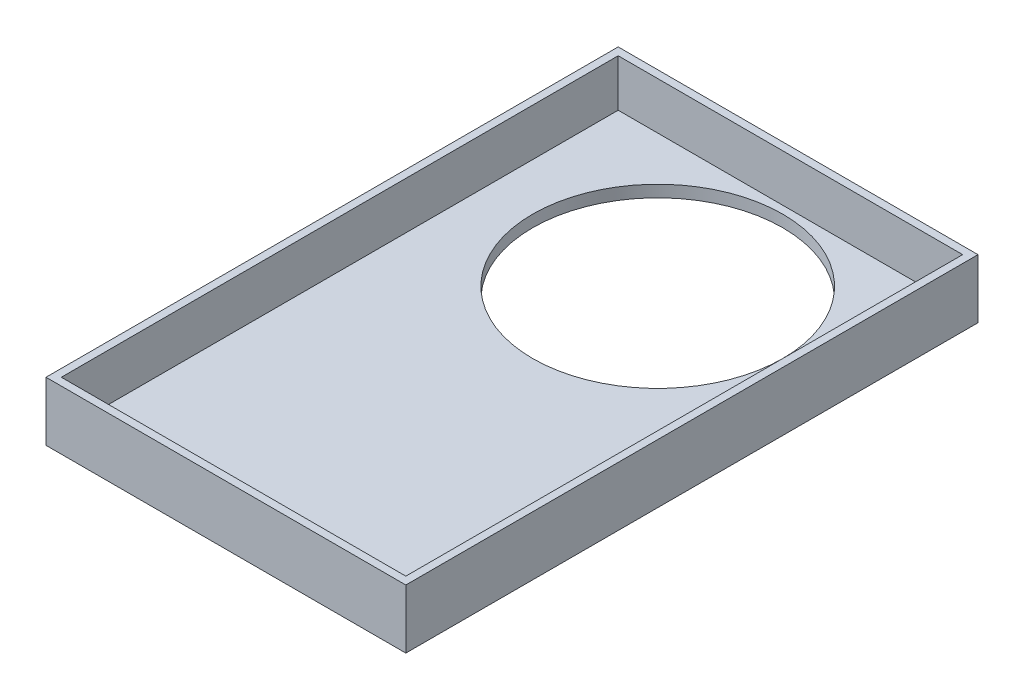
SolidWorks part; units mm, degrees
ref_plane "Front Plane" through (0, 0, 0) normal (0, 0, 1) x (1, 0, 0)
ref_plane "Top Plane" through (0, 0, 0) normal (0, 1, 0) x (1, 0, 0)
ref_plane "Right Plane" through (0, 0, 0) normal (1, 0, 0) x (0, 0, -1)
sketch "Sketch1" plane through (0, 0, 0) normal (0, 1, 0) x (1, 0, 0)
  line L0 (14.25, -10.5939) -> (15.25, -10.5939) construction
  line L5 (-14.25, 12.6561) -> (14.25, 12.6561)
  line L6 (-14.25, 12.6561) -> (-14.25, -33.8439)
  line L11 (-14.25, -33.8439) -> (14.25, -33.8439)
  line L12 (14.25, 12.6561) -> (14.25, -33.8439)
  line L13 (14.75, -10.5939) -> (14.75, 7.2968) construction
  line L15 (15.25, 12.8561) -> (44.15, 12.8561)
  line L16 (15.25, 12.8561) -> (15.25, -34.0439)
  line L17 (15.25, -34.0439) -> (44.15, -34.0439)
  line L18 (44.15, 12.8561) -> (44.15, -34.0439)
  line L19 (-15.25, 13.6561) -> (46.15, 13.6561)
  line L20 (-15.25, 13.6561) -> (-15.25, -34.8439)
  line L21 (-15.25, -34.8439) -> (46.15, -34.8439)
  line L22 (46.15, 13.6561) -> (46.15, -34.8439)
  circle A0 centre (0, 0) radius 10.25
  dimension "D1" = 28.5
  dimension "D2" = 14.25
  dimension "D3" = 46.5
  dimension "D4" = 1
  dimension "D5" = 28.9
  dimension "D6" = 46.9
  dimension "D7" = 1
  dimension "D8" = 1
  dimension "D9" = 1
  dimension "D10" = 2
extrude "Boss-Extrude1" add sketch "Sketch1" along normal blind 35.7 contours L22 L19 L20 L21 L5 L12 L11 L6 L15 L18 L17 L16
sketch "Sketch2" plane through (0, 35.7, 0) normal (0, 1, 0) x (1, 0, 0)
  line L0 (-15.25, -34.8439) -> (46.15, -34.8439) construction
  line L1 (46.15, 13.6561) -> (16.25, 13.6561)
  line L2 (46.15, 13.6561) -> (46.15, -34.8439)
  line L3 (46.15, -34.8439) -> (16.25, -34.8439)
  line L4 (16.25, 13.6561) -> (16.25, -34.8439)
extrude "Cut-Extrude1" cut sketch "Sketch2" against normal through all
sketch "Sketch3" plane through (0, 35.7, 0) normal (0, 1, 0) x (1, 0, 0)
  line L0 (-14.25, 12.6561) -> (14.25, 12.6561) construction
  line L1 (-14.6, 13.0061) -> (14.6, 13.0061)
  line L2 (-14.6, 13.0061) -> (-14.6, -34.1939)
  line L3 (-14.6, -34.1939) -> (14.6, -34.1939)
  line L4 (14.6, 13.0061) -> (14.6, -34.1939)
  line L5 (-14.25, 12.6561) -> (-14.25, -33.8439) construction
  line L6 (14.25, 12.6561) -> (14.25, -33.8439) construction
  line L7 (-14.25, -33.8439) -> (14.25, -33.8439) construction
  dimension "D1" = 0.35
  dimension "D2" = 0.35
  dimension "D3" = 0.35
  dimension "D4" = 0.35
extrude "Cut-Extrude2" cut sketch "Sketch3" against normal through all
sketch "Sketch4" plane through (0, 0, 0) normal (0, 1, 0) x (1, 0, 0)
  line L1 (-14.6, 13.0061) -> (14.6, 13.0061)
  line L2 (-14.6, 13.0061) -> (-14.6, -34.1939)
  line L3 (-14.6, -34.1939) -> (14.6, -34.1939)
  line L4 (14.6, 13.0061) -> (14.6, -34.1939)
  circle A1 centre (0, 1.7561) radius 10.6
  dimension "D1" = 21.2
  dimension "D2" = 11.25
  dimension "D3" = 14.6
extrude "Boss-Extrude2" add sketch "Sketch4" along normal blind 1
sketch "Sketch6" plane through (0, 35.7, 0) normal (0, 1, 0) x (1, 0, 0)
  line L0 (-15.25, -34.8439) -> (16.25, -34.8439) construction
  line L1 (16.25, 13.6561) -> (15.25, 13.6561)
  line L2 (16.25, 13.6561) -> (16.25, -34.8439)
  line L3 (16.25, -34.8439) -> (15.25, -34.8439)
  line L4 (15.25, 13.6561) -> (15.25, -34.8439)
extrude "Cut-Extrude3" cut sketch "Sketch6" against normal through all
sketch "Sketch7" plane through (0, 0, 34.8439) normal (0, 0, 1) x (1, 0, 0)
  line L0 (15.25, 0) -> (15.25, 35.7) construction
  line L1 (-15.25, 35.7) -> (15.25, 35.7)
  line L2 (-15.25, 35.7) -> (-15.25, 5)
  line L3 (-15.25, 5) -> (15.25, 5)
  line L4 (15.25, 35.7) -> (15.25, 5)
  line L5 (-15.25, 0) -> (15.25, 0) construction
  dimension "D1" = 5
extrude "Cut-Extrude4" cut sketch "Sketch7" against normal through all
